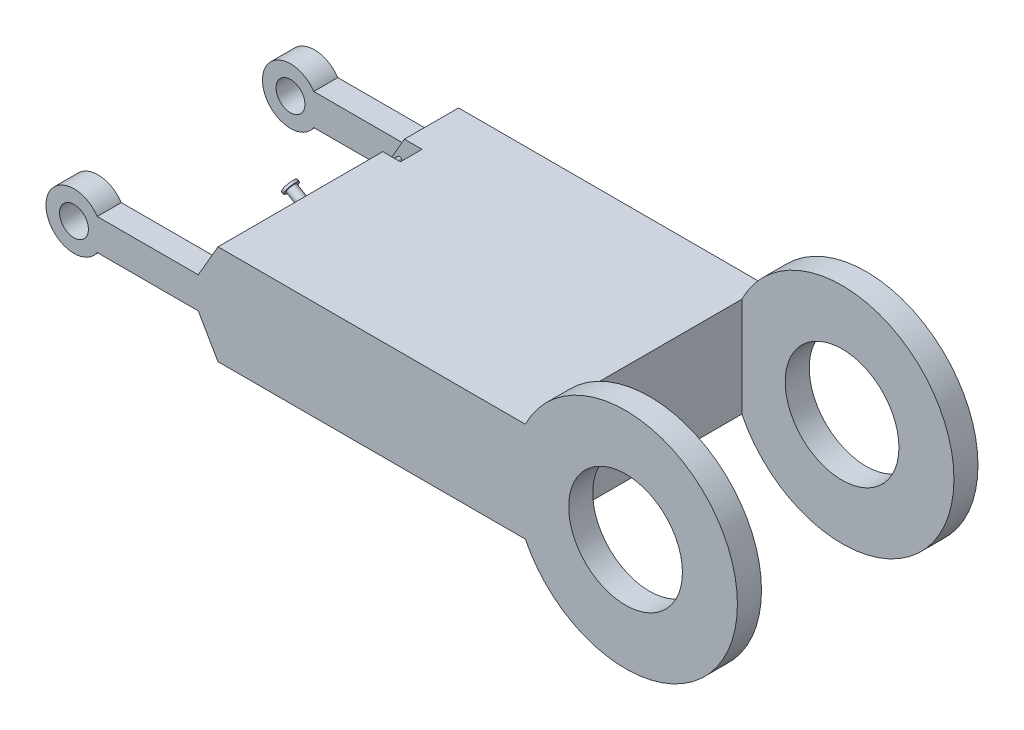
SolidWorks part; units mm, degrees
other "Markup1"
sketch "Sketch23" plane through (-68.476, 46.5083, -50) normal (-0.9084, 0.417, -0.0319) x (-0.0904, -0.1211, 0.9885)
other "Markup2"
sketch "Sketch31" plane through (-68.476, 46.5083, 50) normal (-0.8863, 0.1717, 0.4301) x (0.4407, 0.0276, 0.8972)
ref_plane "Front Plane" through (0, 0, 0) normal (0, 0, 1) x (1, 0, 0)
ref_plane "Top Plane" through (0, 0, 0) normal (0, 1, 0) x (1, 0, 0)
ref_plane "Right Plane" through (0, 0, 0) normal (1, 0, 0) x (0, 0, -1)
sketch "Sketch1" plane through (0, 0, 0) normal (0, 0, 1) x (1, 0, 0)
  line L0 (0, 0) -> (183.521, 0) construction
  line L1 (0, 0) -> (11.9418, 20.6839)
  line L2 (11.9418, 20.6839) -> (139.7028, 20.6839)
  line L3 (139.7028, 20.6839) -> (139.7028, -20.6839)
  line L4 (11.9418, -20.6839) -> (139.7028, -20.6839)
  line L5 (0, 0) -> (11.9418, -20.6839)
  point P7 (139.7028, 0)
  dimension "D1" = 60
extrude "Boss-Extrude4" add sketch "Sketch1" along normal blind 40
sketch "Sketch4" plane through (0, 0, 40) normal (0, 0, 1) x (1, 0, 0)
  line L0 (11.9418, 20.6839) -> (139.7028, 20.6839)
  line L1 (0, 0) -> (-87.1197, 0) construction
  line L2 (139.7028, -20.6839) -> (11.9418, -20.6839)
  line L3 (11.9418, -20.6839) -> (3.7528, -6.5)
  line L4 (0, 0) -> (11.9418, -20.6839) construction
  line L5 (3.7528, -6.5) -> (-38.2472, -6.5)
  line L6 (-38.2472, -6.5) -> (3.7528, -6.5)
  line L7 (3.7528, 6.5) -> (-38.2472, 6.5)
  line L8 (11.9418, 20.6839) -> (0, 0) construction
  arc A2 (139.7028, -20.6839) -> (139.7028, 20.6839) centre (181.3585, 0) ccw
  circle A3 centre (181.3585, 0) radius 23.6439
  circle A4 centre (-47.9201, 0) radius 11.6539
  circle A5 centre (-47.9201, 0) radius 6
  dimension "D1" = 42
  dimension "D2" = 13
  dimension "D3" = 120
  dimension "D4" = 47.9201
  dimension "D5" = 41.3677
extrude "Boss-Extrude5" add sketch "Sketch4" along normal blind 10
mirror "Mirror2" about plane through (0, 0, 0) normal (0, 0, 1) of bodies 105
ref_plane "Plane2" through (0, 0, -23) normal (0, 0, 1) x (1, 0, 0)
sketch "Sketch19" plane through (0, 0, -23) normal (0, 0, 1) x (1, 0, 0)
  circle A0 centre (9.8749, 12.4213) radius 12.5
  circle A1 centre (9.8749, 12.4213) radius 1
extrude "Cut-Extrude2" cut sketch "Sketch19" against normal mid plane 9
sketch "Sketch21" plane through (0, 0, 0) normal (-0.866, 0.5, 0) x (0, 0, 1)
  circle A1 centre (7, 11.9418) radius 2
extrude "Boss-Extrude7" add sketch "Sketch21" along normal blind 8.5
sketch "Sketch24" plane through (0, 0, 0) normal (-0.866, -0.5, 0) x (0, 0, 1)
  circle A0 centre (13, -11.9418) radius 2
extrude "Boss-Extrude8" add sketch "Sketch24" along normal blind 8.5
ref_plane "Plane4" through (0, 0, -17) normal (0, 0, 1) x (1, 0, 0)
sketch "Sketch26" plane through (0, 0, -17) normal (0, 0, 1) x (1, 0, 0)
  circle A0 centre (9.8749, -12.4213) radius 12.5
extrude "Cut-Extrude3" cut sketch "Sketch26" against normal mid plane 9
sketch "Sketch32" plane through (0, 0, -17) normal (0, 0, 1) x (1, 0, 0)
  circle A0 centre (9.8778, -12.4264) radius 1.5
extrude "Boss-Extrude10" add sketch "Sketch32" along direction (0, 0, 1) on the side of the normal mid plane 9 separate body
sketch "Sketch33" plane through (-7.3612, 4.25, 0) normal (-0.866, 0.5, 0) x (0, 0, 1)
  circle A0 centre (7, 11.9418) radius 3
extrude "Boss-Extrude11" add sketch "Sketch33" against normal blind 1
sketch "Sketch34" plane through (-7.3612, -4.25, 0) normal (-0.866, -0.5, 0) x (0, 0, 1)
  circle A0 centre (13, -11.9418) radius 3
extrude "Boss-Extrude12" add sketch "Sketch34" against normal blind 1
